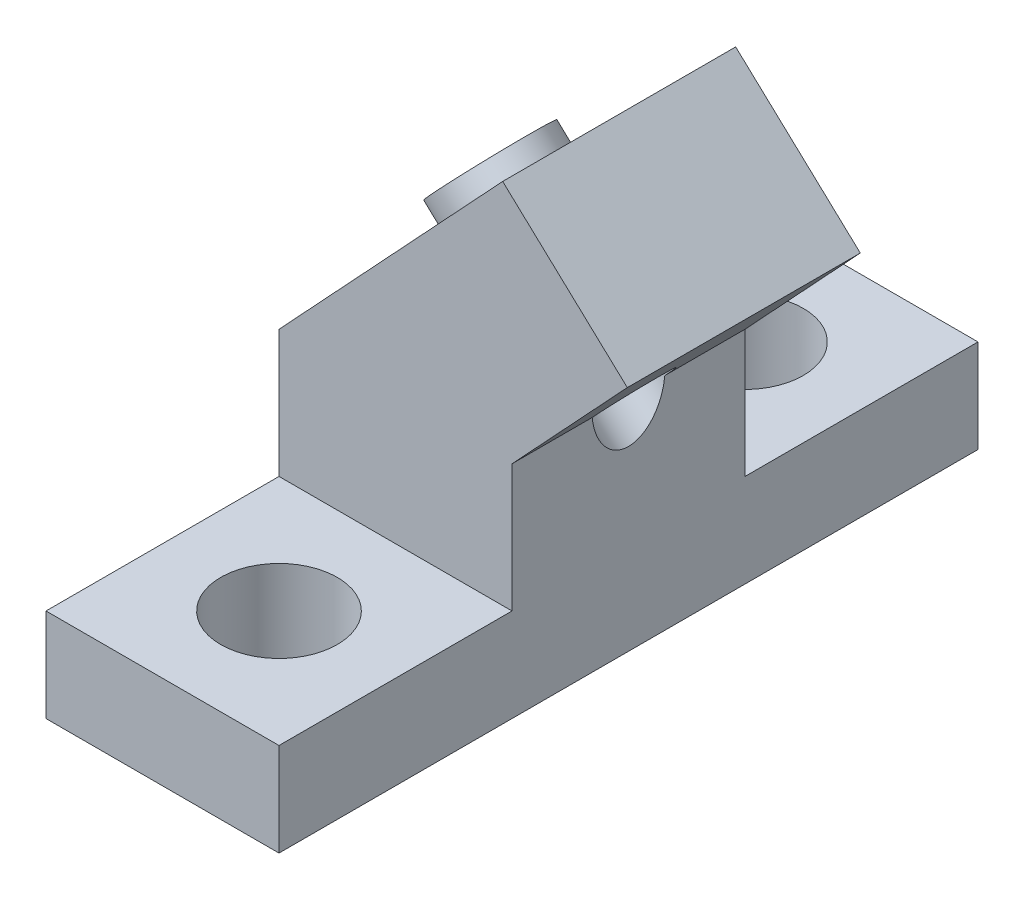
SolidWorks part; units mm, degrees
ref_plane "Front Plane" through (0, 0, 0) normal (0, 0, 1) x (1, 0, 0)
ref_plane "Top Plane" through (0, 0, 0) normal (0, 1, 0) x (1, 0, 0)
ref_plane "Right Plane" through (0, 0, 0) normal (1, 0, 0) x (0, 0, -1)
sketch "Sketch7" plane through (0, 0, 0) normal (0, 0, 1) x (1, 0, 0)
  line L0 (0, 12.0277) -> (12.192, 25.102)
  line L1 (0, 0) -> (12.7, 0)
  line L2 (0, 0) -> (0, 12.0277)
  line L4 (12.7, 0) -> (12.7, 12.0277)
  line L5 (12.7, 12.0277) -> (24.892, 25.102)
  line L6 (12.192, 25.102) -> (24.892, 25.102)
  line L7 (12.7, 12.0277) -> (31.8633, 12.0277) construction
  line L8 (6.096, 18.5649) -> (5.1672, 19.431) construction
  point P11 (18.796, 18.5649)
  dimension "D1" = 47
  dimension "D2" = 1.27
  dimension "D3" = 6.096
  dimension "D4" = 12.7
  dimension "D5" = 19.431
extrude "Boss-Extrude3" add sketch "Sketch7" along normal blind 12.7
sketch "Sketch8" plane through (-5.9992, 5.5943, 0) normal (-0.7314, 0.682, 0) x (0, 0, 1)
  line L0 (6.35, 26.6734) -> (6.35, 8.7965) construction
  line L1 (12.7, 26.6734) -> (0, 26.6734) construction
  line L2 (12.7, 8.7965) -> (0, 8.7965) construction
  circle A0 centre (6.35, 17.7349) radius 2
  point P9 (6.35, 17.7349)
  dimension "D1" = 4
extrude "Cut-Extrude5" cut sketch "Sketch8" against normal blind 12.7
sketch "Sketch9" plane through (0, 0, 12.7) normal (0, 0, 1) x (1, 0, 0)
  line L5 (12.192, 25.102) -> (18.985, 18.7675)
  line L6 (12.7, 12.0277) -> (24.892, 25.102) construction
  line L8 (12.192, 25.102) -> (24.892, 25.102)
  line L9 (24.892, 25.102) -> (18.985, 18.7675)
  line L10 (12.192, 25.102) -> (0, 12.0277) construction
extrude "Cut-Extrude7" cut sketch "Sketch9" against normal blind 12.7
sketch "Sketch10" plane through (0, 0, 12.7) normal (0, 0, 1) x (1, 0, 0)
  line L0 (12.7, 0) -> (12.7, 12.0277) construction
  line L1 (0, 0) -> (12.7, 0)
  line L2 (0, 0) -> (0, 5.08)
  line L3 (0, 5.08) -> (12.7, 5.08)
  line L4 (12.7, 0) -> (12.7, 5.08)
  dimension "D1" = 5.08
extrude "Boss-Extrude4" add sketch "Sketch10" along normal blind 12.7
sketch "Sketch11" plane through (0, 5.08, 0) normal (0, 1, 0) x (1, 0, 0)
  line L0 (0, -19.05) -> (12.7, -19.05) construction
  line L1 (0, -25.4) -> (0, -12.7) construction
  line L2 (12.7, -25.4) -> (12.7, -12.7) construction
  circle A0 centre (6.35, -19.05) radius 3.175
  point P10 (6.35, -19.05)
  dimension "D1" = 6.35
extrude "Cut-Extrude8" cut sketch "Sketch11" against normal blind 12.7
ref_plane "Plane2" through (0, 0, 6.35) normal (0, 0, 1) x (1, 0, 0)
mirror "Mirror2" about plane through (0, 0, 6.35) normal (0, 0, 1) of "Boss-Extrude4", "Cut-Extrude8"
sketch "Sketch12" plane through (0, 0, 6.35) normal (0, 0, 1) x (1, 0, 0)
  line L4 (3.8298, 17.9434) -> (7.46, 20.0276) construction
  line L5 (4.732, 17.1022) -> (12.7, 9.6719) construction
sketch "Sketch13" plane through (-5.9992, 5.5943, 0) normal (-0.7314, 0.682, 0) x (0, 0, 1)
  line L0 (6.35, 15.7349) -> (6.35, 19.7349) construction
  circle A0 centre (6.35, 17.7349) radius 3
  circle A1 centre (6.35, 17.7349) radius 2
  circle A2 centre (6.35, 17.7349) radius 2 construction
  dimension "D1" = 6
extrude "Boss-Extrude5" add sketch "Sketch13" along normal blind 1.27
sketch "Sketch14" plane through (-6.928, 6.4605, 0) normal (-0.7314, 0.682, 0) x (0, 0, 1)
  line L0 (6.35, 20.7349) -> (6.35, 14.7349) construction
  line L1 (6.35, -10.4417) -> (6.35, 10.4417) construction
  circle A0 centre (6.35, 17.7349) radius 3 construction
  point P6 (6.35, 17.7349)
sketch "Sketch15" plane through (0, 0, 6.35) normal (0, 0, 1) x (1, 0, 0)
  line L0 (5.1672, 19.431) -> (5.1672, 25.8408) construction
